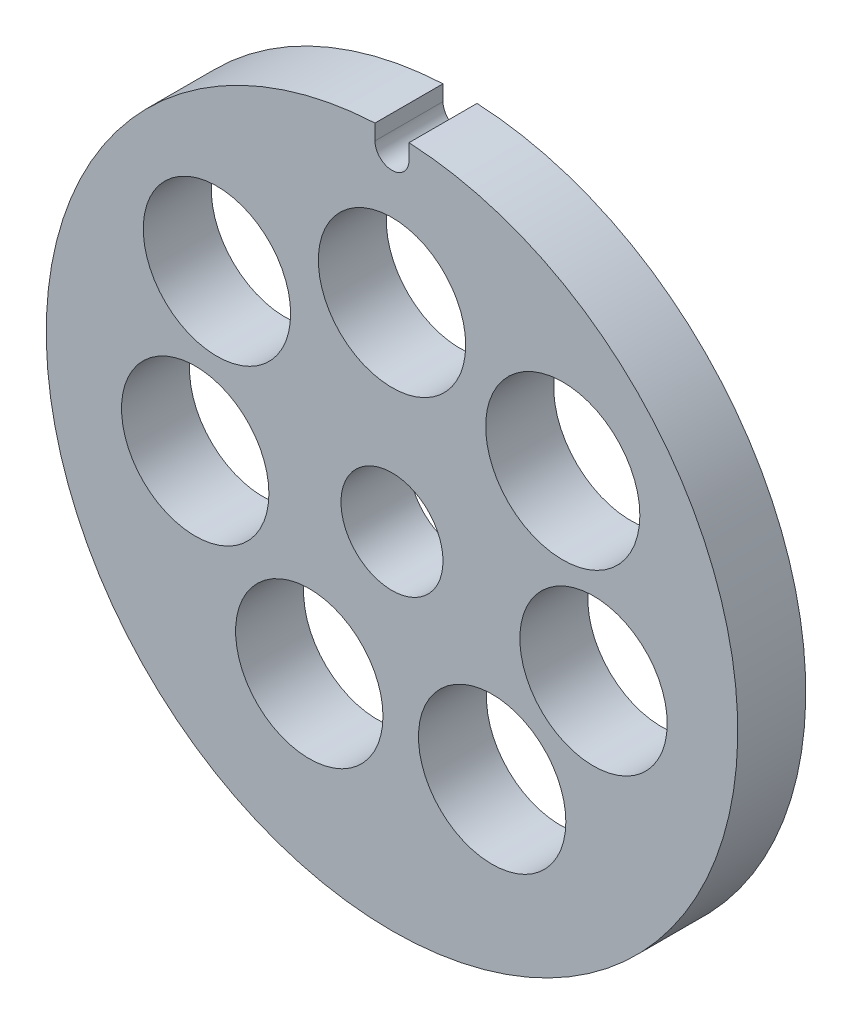
SolidWorks part; units mm, degrees
ref_plane "Płaszczyzna przednia" through (0, 0, 0) normal (0, 0, 1) x (1, 0, 0)
ref_plane "Płaszczyzna górna" through (0, 0, 0) normal (0, 1, 0) x (1, 0, 0)
ref_plane "Płaszczyzna prawa" through (0, 0, 0) normal (1, 0, 0) x (0, 0, -1)
sketch "Szkic1" plane through (0, 0, 0) normal (0, 0, 1) x (1, 0, 0)
  line L0 (-19.7988, 49.0313) -> (-19.7988, 47.6313) construction
  line L1 (-18.2988, 49.0313) -> (-18.2988, 47.6313)
  line L2 (-21.2988, 49.0313) -> (-21.2988, 47.6313)
  circle A0 centre (-19.7988, 18.5313) radius 30.5
  circle A1 centre (-19.7988, 18.5313) radius 4.5
  circle A2 centre (-19.7974, 36.0313) radius 6.5
  circle A3 centre (-4.7352, 30.7018) radius 6.8004
  circle A4 centre (-2.0201, 16.0084) radius 6.5
  circle A5 centre (-10.964, 4.03) radius 6.5
  circle A6 centre (-27.0949, 4.03) radius 6.5
  circle A7 centre (-37.1567, 16.0084) radius 6.5
  circle A8 centre (-35.2402, 30.7018) radius 6.5
  arc A9 (-18.2988, 49.0313) -> (-21.2988, 49.0313) centre (-19.7988, 49.0313) ccw
  arc A10 (-21.2988, 47.6313) -> (-18.2988, 47.6313) centre (-19.7988, 47.6313) ccw
  point P19 (-19.7988, 48.3313)
  dimension "D1" = 61
  dimension "D2" = 9
  dimension "D3" = 13
  dimension "D4" = 17.5
  dimension "D5" = 1.4
  dimension "D6" = 1.5
extrude "Dodanie-wyciągnięcie1" add sketch "Szkic1" along normal blind 6 contours A10 L2 A0 L1 A8 A7 A6 A5 A4 A3 A2 A1
